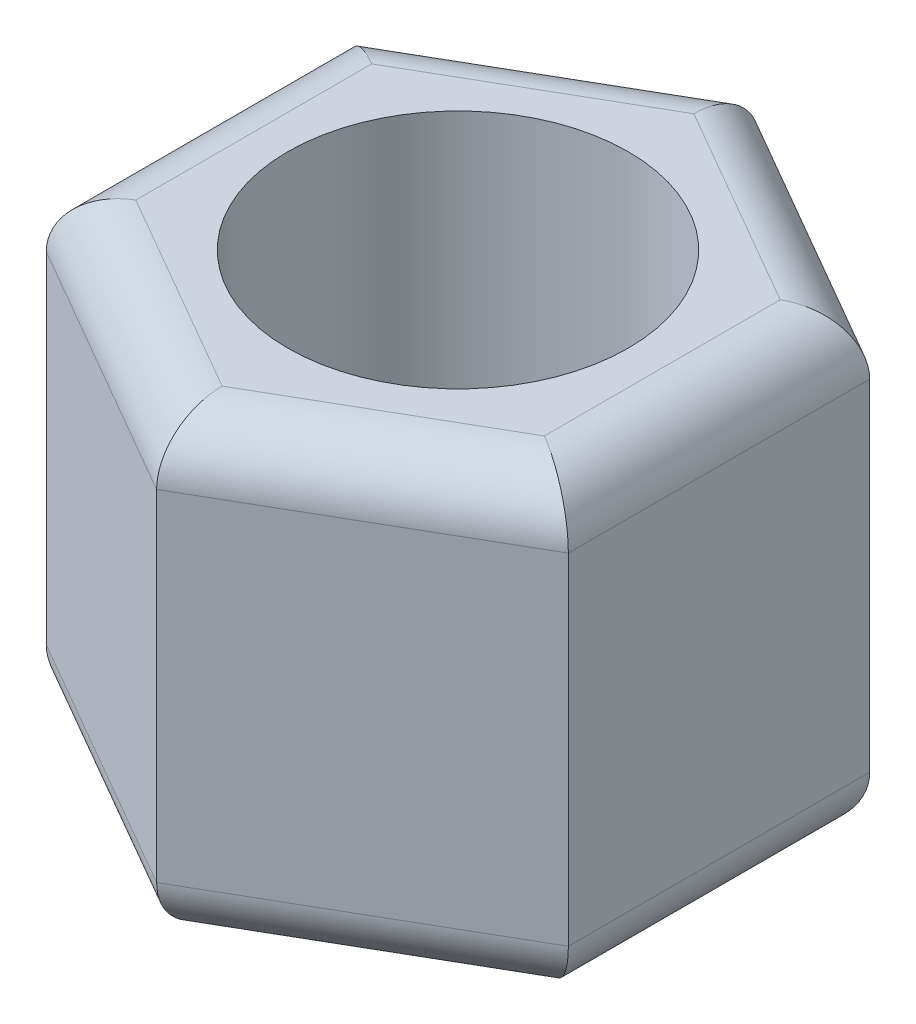
SolidWorks part; units mm, degrees
ref_plane "前视基准面" through (0, 0, 0) normal (0, 0, 1) x (1, 0, 0)
ref_plane "上视基准面" through (0, 0, 0) normal (0, 1, 0) x (1, 0, 0)
ref_plane "右视基准面" through (0, 0, 0) normal (1, 0, 0) x (0, 0, -1)
sketch "草图1" plane through (0, 0, 0) normal (0, 1, 0) x (1, 0, 0)
  line L1 (2.3, -1.3279) -> (2.3, 1.3279)
  line L2 (2.3, 1.3279) -> (0, 2.6558)
  line L3 (0, 2.6558) -> (-2.3, 1.3279)
  line L4 (-2.3, 1.3279) -> (-2.3, -1.3279)
  line L5 (-2.3, -1.3279) -> (0, -2.6558)
  line L6 (0, -2.6558) -> (2.3, -1.3279)
  circle A0 centre (0, 0) radius 2.3 construction
  circle A1 centre (0, 0) radius 1.5
  dimension "D2" = 3
  dimension "D1" = 4.6
extrude "凸台-拉伸1" add sketch "草图1" along normal blind 4
fillet "圆角1" radius 0.5 12 edges at (-1.15, 4, 1.9919) (-2.3, 4, 0) (-1.15, 4, -1.9919) (1.15, 4, -1.9919) (2.3, 4, 0) (1.15, 4, 1.9919) (-1.15, 0, 1.9919) (1.15, 0, 1.9919) (2.3, 0, 0) (1.15, 0, -1.9919) (-1.15, 0, -1.9919) (-2.3, 0, 0)
